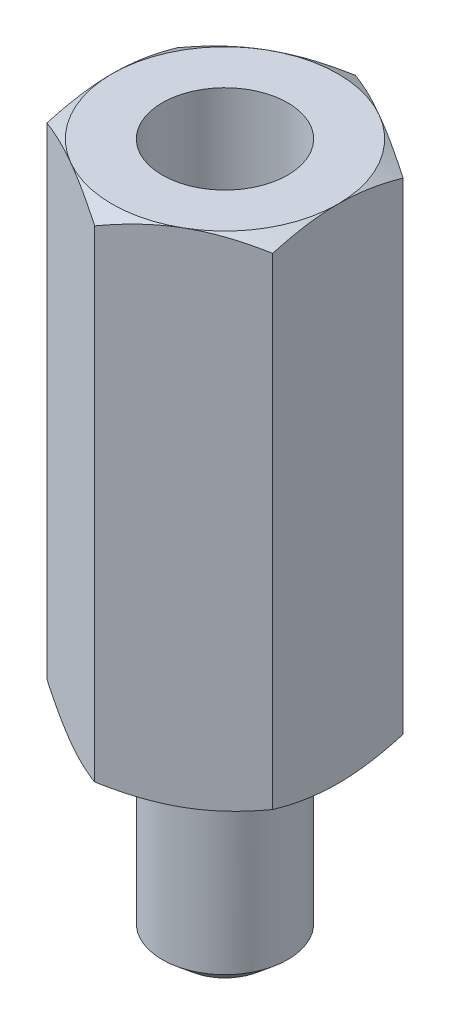
SolidWorks part; units mm, degrees
ref_plane "Front Plane" through (0, 0, 0) normal (0, 0, 1) x (1, 0, 0)
ref_plane "Top Plane" through (0, 0, 0) normal (0, 1, 0) x (1, 0, 0)
ref_plane "Right Plane" through (0, 0, 0) normal (1, 0, 0) x (0, 0, -1)
sketch "Sketch1" plane through (0, 0, 0) normal (0, 1, 0) x (1, 0, 0)
  line L1 (0, 2.5981) -> (-2.25, 1.299)
  line L2 (-2.25, 1.299) -> (-2.25, -1.299)
  line L3 (-2.25, -1.299) -> (0, -2.5981)
  line L4 (0, -2.5981) -> (2.25, -1.299)
  line L5 (2.25, -1.299) -> (2.25, 1.299)
  line L6 (2.25, 1.299) -> (0, 2.5981)
  circle A0 centre (0, 0) radius 2.25 construction
  dimension "D1" = 4.5
extrude "Boss-Extrude1" add sketch "Sketch1" along normal blind 10
sketch "Sketch2" plane through (0, 10, 0) normal (0, 1, 0) x (1, 0, 0)
  line L0 (0, 2.5981) -> (-2.25, 1.299) construction
  circle A0 centre (0, 0) radius 2.25
extrude "Cut-Extrude1" cut sketch "Sketch2" against normal through all draft 60 flip side to cut
sketch "Sketch3" plane through (0, 0, 0) normal (0, -1, 0) x (1, 0, 0)
  circle A0 centre (0, 0) radius 2.25
extrude "Cut-Extrude2" cut sketch "Sketch3" against normal through all draft 60 flip side to cut
sketch "Sketch4" plane through (0, 10, 0) normal (0, 1, 0) x (1, 0, 0)
  circle A0 centre (0, 0) radius 1.25
  dimension "D1" = 2.5
extrude "Cut-Extrude3" cut sketch "Sketch4" against normal blind 4.8
sketch "Sketch5" plane through (0, 0, 0) normal (0, -1, 0) x (1, 0, 0)
  circle A0 centre (0, 0) radius 1.25
  dimension "D1" = 2.5
extrude "Boss-Extrude2" add sketch "Sketch5" along normal blind 3.9
chamfer "Chamfer1" distance 0.36 angle 50 1 edges at (0, -3.9, -1.25)
